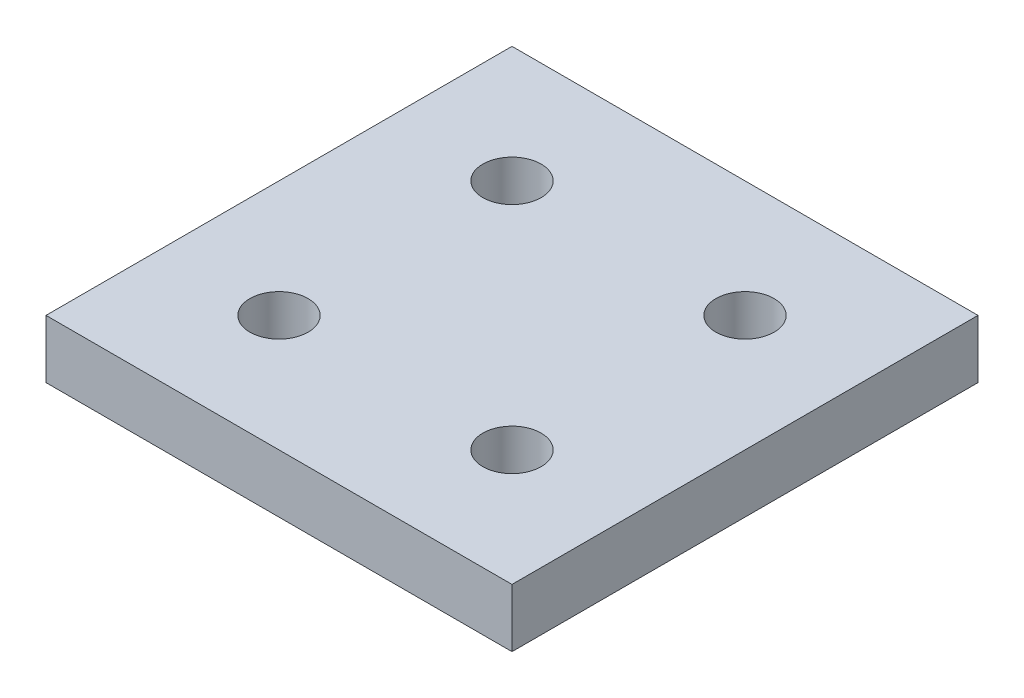
SolidWorks part; units mm, degrees
material "Plain Carbon Steel"
ref_plane "Front Plane" through (0, 0, 0) normal (0, 0, 1) x (1, 0, 0)
ref_plane "Top Plane" through (0, 0, 0) normal (0, 1, 0) x (1, 0, 0)
ref_plane "Right Plane" through (0, 0, 0) normal (1, 0, 0) x (0, 0, -1)
sketch "Sketch1" plane through (0, 0, 0) normal (0, 1, 0) x (1, 0, 0)
  line L1 (0, 0) -> (101.6, 0)
  line L2 (0, 0) -> (0, 101.6)
  line L3 (0, 101.6) -> (101.6, 101.6)
  line L4 (101.6, 0) -> (101.6, 101.6)
  dimension "D1" = 101.6
  dimension "D2" = 101.6
extrude "Boss-Extrude1" add sketch "Sketch1" along normal blind 12.7
hole_wizard "1/2 (0.5) Diameter Hole1" positions "3DSketch1" profile "Sketch2" hole size "1/2" standard "ANSI Inch" end condition through all
sketch3d "3DSketch1"
  line L0 (0, 12.7, -101.6) -> (0, 12.7, 0) construction
  line L1 (101.6, 12.7, -101.6) -> (0, 12.7, -101.6) construction
  line L2 (0, 12.7, 0) -> (101.6, 12.7, 0) construction
  line L3 (101.6, 12.7, 0) -> (101.6, 12.7, -101.6) construction
  point P0 (25.4, 12.7, -25.4)
  point P2 (25.4, 12.7, -76.2)
  point P4 (76.2, 12.7, -76.2)
  point P6 (76.2, 12.7, -25.4)
  dimension "D1" = 25.4
  dimension "D2" = 76.2
  dimension "D3" = 25.4
  dimension "D4" = 25.4
  dimension "D5" = 25.4
  dimension "D6" = 25.4
  dimension "D7" = 25.4
  dimension "D8" = 25.4
sketch "Sketch2" plane through (25.4, 12.7, -25.4) normal (1, 0, 0) x (0, 0, 1)
  line L0 (0, 0) -> (0, 12.7)
  line L1 (0, 12.7) -> (6.35, 12.7)
  line L2 (6.35, 12.7) -> (6.35, 0)
  line L5 (6.35, 0) -> (0, 0)
  line L11 (0, -6.35) -> (0, 107.95) construction
  dimension "Thru Hole Dia." = 12.7
  dimension "Thru Hole Depth" = 12.7
